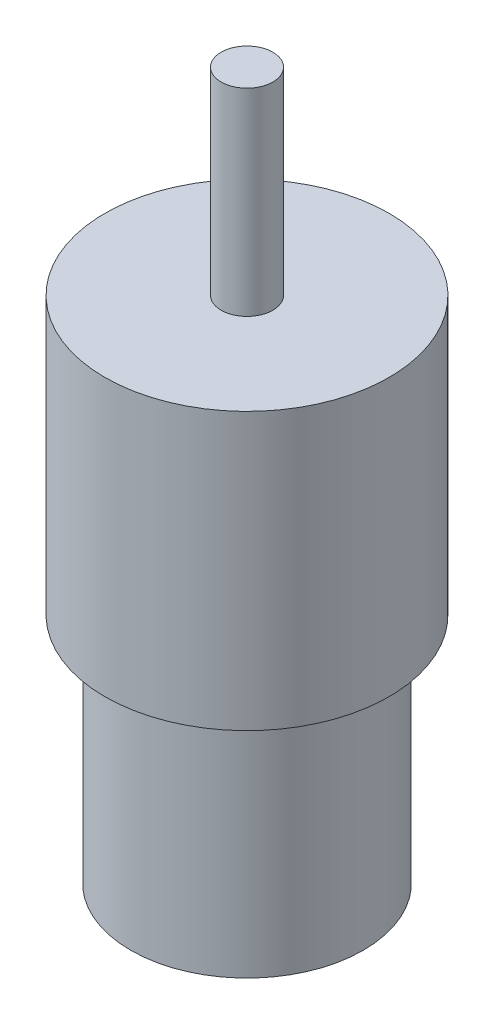
SolidWorks part; units mm, degrees
ref_plane "Alzado" through (0, 0, 0) normal (0, 0, 1) x (1, 0, 0)
ref_plane "Planta" through (0, 0, 0) normal (0, 1, 0) x (1, 0, 0)
ref_plane "Vista lateral" through (0, 0, 0) normal (1, 0, 0) x (0, 0, -1)
sketch "Croquis1" plane through (0, 0, 0) normal (0, 1, 0) x (1, 0, 0)
  circle A0 centre (0, 0) radius 11
  dimension "D1" = 22
extrude "Saliente-Extruir1" add sketch "Croquis1" along normal blind 21.4
sketch "Croquis2" plane through (0, 21.4, 0) normal (0, 1, 0) x (1, 0, 0)
  circle A0 centre (0, 0) radius 2
  dimension "D1" = 4
extrude "Saliente-Extruir2" add sketch "Croquis2" along normal blind 15.3
sketch "Croquis3" plane through (0, 0, 0) normal (0, -1, 0) x (1, 0, 0)
  circle A0 centre (0, 0) radius 9
  dimension "D1" = 18
extrude "Saliente-Extruir3" add sketch "Croquis3" along normal blind 18
sketch "Croquis4" plane through (0, 21.4, 0) normal (0, 1, 0) x (1, 0, 0)
  line L1 (9, -9) -> (-9, -9)
  line L2 (9, -9) -> (9, 9)
  line L3 (9, 9) -> (-9, 9)
  line L4 (-9, -9) -> (-9, 9)
  line L5 (9, -9) -> (-9, 9) construction
  line L6 (9, 9) -> (-9, -9) construction
  circle A1 centre (0, 0) radius 16
  circle A2 centre (0, 0) radius 11 construction
  point P0 (0, 0)
  dimension "D1" = 5
  dimension "D2" = 18
extrude "Cortar-Extruir1" [suppressed] cut sketch "Croquis4" against normal through all
